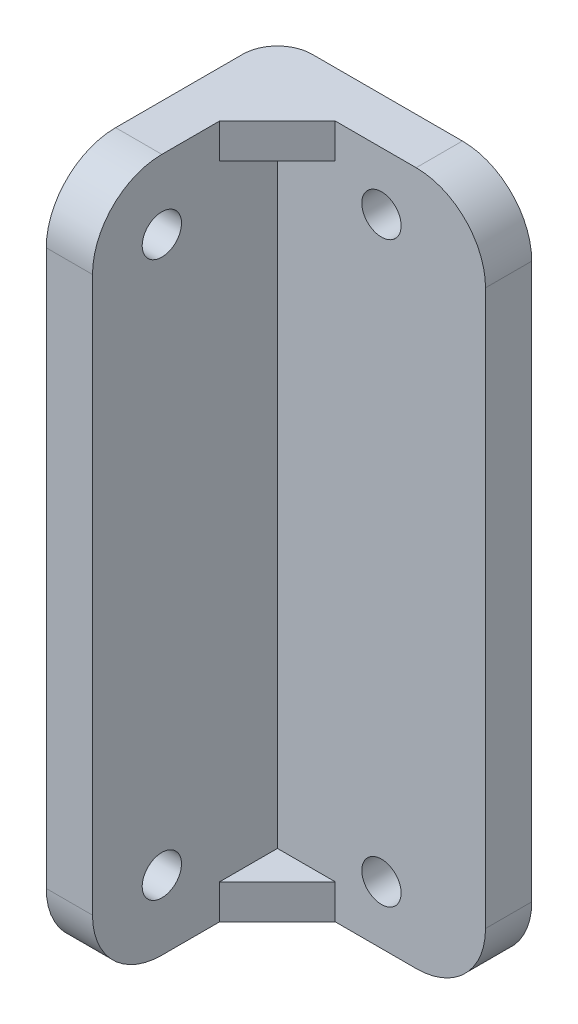
SolidWorks part; units mm, degrees
ref_plane "Front Plane" through (0, 0, 0) normal (0, 0, 1) x (1, 0, 0)
ref_plane "Top Plane" through (0, 0, 0) normal (0, 1, 0) x (1, 0, 0)
ref_plane "Right Plane" through (0, 0, 0) normal (1, 0, 0) x (0, 0, -1)
sketch "Sketch1" plane through (0, 0, 0) normal (0, 0, 1) x (1, 0, 0)
  line L0 (0, 50) -> (0, 0)
  line L2 (9, -5) -> (-9, -5)
  line L3 (9, -5) -> (9, 55)
  line L4 (9, 55) -> (-9, 55)
  line L5 (-9, -5) -> (-9, 55)
  line L6 (9, -5) -> (-9, 55) construction
  line L7 (9, 55) -> (-9, -5) construction
  circle A0 centre (0, 0) radius 1.7
  circle A1 centre (0, 50) radius 1.7
  point P5 (0, 25)
  dimension "D1" = 3.4
  dimension "D2" = 3.4
  dimension "D3" = 50
  dimension "D4" = 60
  dimension "D5" = 18
extrude "Boss-Extrude1" add sketch "Sketch1" along normal blind 4
sketch "Sketch2" plane through (-9, 0, 0) normal (-1, 0, 0) x (0, 0, 1)
  line L0 (7, 55) -> (7, -5) construction
  line L1 (0, 55) -> (14, 55)
  line L2 (0, 55) -> (0, -5)
  line L3 (0, -5) -> (14, -5)
  line L4 (20, 49) -> (20, 1)
  arc A0 (20, 1) -> (14, -5) centre (14, 1) cw
  arc A1 (20, 49) -> (14, 55) centre (14, 49) ccw
  circle A2 centre (14, 49) radius 1.7
  circle A3 centre (14, 1) radius 1.7
  point P11 (20, 55)
  dimension "D3" = 6
  dimension "D4" = 3.4
  dimension "D5" = 3.4
  dimension "D1" = 60
  dimension "D2" = 20
extrude "Boss-Extrude2" add sketch "Sketch2" along normal blind 4
fillet "Fillet1" radius 6 2 edges at (9, -5, 2) (9, 55, 2)
ref_plane "Plane1" through (0, 25, 0) normal (0, 1, 0) x (1, 0, 0)
sketch "Sketch3" plane through (0, 55, 0) normal (0, 1, 0) x (1, 0, 0)
  line L0 (-4, -4) -> (-9, -9)
  line L1 (-9, -4) -> (-4, -4)
  line L2 (-9, -4) -> (-9, -9)
  dimension "D1" = 5
extrude "Boss-Extrude3" add sketch "Sketch3" against normal blind 3
mirror "Mirror1" about plane through (0, 25, 0) normal (0, 1, 0) of "Boss-Extrude3"
fillet "Fillet2" radius 3 1 edges at (-13, 25, 0)
